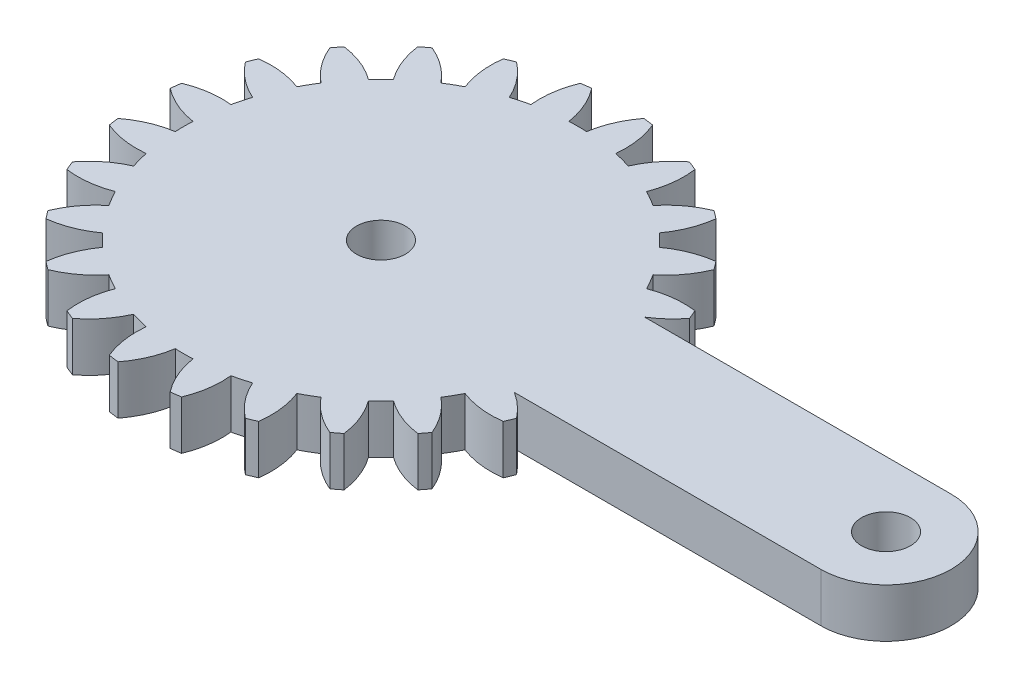
SolidWorks part; units mm, degrees
ref_plane "Front" through (0, 0, 0) normal (0, 0, 1) x (1, 0, 0)
ref_plane "Top" through (0, 0, 0) normal (0, 1, 0) x (1, 0, 0)
ref_plane "Right" through (0, 0, 0) normal (1, 0, 0) x (0, 0, -1)
sketch "Sketch1" plane through (0, 0, 0) normal (0, 1, 0) x (1, 0, 0)
  line L0 (11.068, -3.7704) -> (29.88, -3.7704)
  line L1 (29.88, 4.2296) -> (11.068, 4.2296)
  circle A0 centre (29.88, 0.2296) radius 1.5
  arc A1 (12.5081, -5.0775) -> (11.068, -3.7704) centre (8.218, -8.3571) ccw
  arc A2 (12.2692, -5.6542) -> (12.5081, -5.0775) centre (-1.12, 0.2296) ccw
  arc A3 (9.6134, -5.3407) -> (12.2692, -5.6542) centre (11.5547, -0.3017) ccw
  arc A4 (9.0707, -6.2807) -> (9.6134, -5.3407) centre (-1.12, 0.2296) ccw
  arc A5 (10.6701, -8.4239) -> (9.0707, -6.2807) centre (5.6774, -10.4814) ccw
  arc A6 (10.2901, -8.9191) -> (10.6701, -8.4239) centre (-1.12, 0.2296) ccw
  arc A7 (7.806, -7.9289) -> (10.2901, -8.9191) centre (10.9853, -3.564) ccw
  arc A8 (7.0385, -8.6964) -> (7.806, -7.9289) centre (-1.12, 0.2296) ccw
  arc A9 (8.0287, -11.1806) -> (7.0385, -8.6964) centre (2.6736, -11.8757) ccw
  arc A10 (7.5335, -11.5605) -> (8.0287, -11.1806) centre (-1.12, 0.2296) ccw
  arc A11 (5.3903, -9.9611) -> (7.5335, -11.5605) centre (9.591, -6.5678) ccw
  arc A12 (4.4502, -10.5038) -> (5.3903, -9.9611) centre (-1.12, 0.2296) ccw
  arc A13 (4.7638, -13.1596) -> (4.4502, -10.5038) centre (-0.5887, -12.4451) ccw
  arc A14 (4.1871, -13.3985) -> (4.7638, -13.1596) centre (-1.12, 0.2296) ccw
  arc A15 (2.5309, -11.2988) -> (4.1871, -13.3985) centre (7.4667, -9.1084) ccw
  arc A16 (1.4824, -11.5798) -> (2.5309, -11.2988) centre (-1.12, 0.2296) ccw
  arc A17 (1.0979, -14.2262) -> (1.4824, -11.5798) centre (-3.8873, -12.1507) ccw
  arc A18 (0.4791, -14.3077) -> (1.0979, -14.2262) centre (-1.12, 0.2296) ccw
  arc A19 (-0.5773, -11.851) -> (0.4791, -14.3077) centre (4.7572, -11.0127) ccw
  arc A20 (-1.6627, -11.851) -> (-0.5773, -11.851) centre (-1.12, 0.2296) ccw
  arc A21 (-2.7191, -14.3077) -> (-1.6627, -11.851) centre (-6.9973, -11.0127) ccw
  arc A22 (-3.338, -14.2262) -> (-2.7191, -14.3077) centre (-1.12, 0.2296) ccw
  arc A23 (-3.7225, -11.5798) -> (-3.338, -14.2262) centre (1.6473, -12.1507) ccw
  arc A24 (-4.7709, -11.2988) -> (-3.7225, -11.5798) centre (-1.12, 0.2296) ccw
  arc A25 (-6.4272, -13.3985) -> (-4.7709, -11.2988) centre (-9.7067, -9.1084) ccw
  arc A26 (-7.0038, -13.1596) -> (-6.4272, -13.3985) centre (-1.12, 0.2296) ccw
  arc A27 (-6.6903, -10.5038) -> (-7.0038, -13.1596) centre (-1.6513, -12.4451) ccw
  arc A28 (-7.6303, -9.9611) -> (-6.6903, -10.5038) centre (-1.12, 0.2296) ccw
  arc A29 (-9.7735, -11.5605) -> (-7.6303, -9.9611) centre (-11.831, -6.5678) ccw
  arc A30 (-10.2687, -11.1806) -> (-9.7735, -11.5605) centre (-1.12, 0.2296) ccw
  arc A31 (-9.2785, -8.6964) -> (-10.2687, -11.1806) centre (-4.9137, -11.8757) ccw
  arc A32 (-10.046, -7.9289) -> (-9.2785, -8.6964) centre (-1.12, 0.2296) ccw
  arc A33 (-12.5302, -8.9191) -> (-10.046, -7.9289) centre (-13.2254, -3.564) ccw
  arc A34 (-12.9102, -8.4239) -> (-12.5302, -8.9191) centre (-1.12, 0.2296) ccw
  arc A35 (-11.3107, -6.2807) -> (-12.9102, -8.4239) centre (-7.9175, -10.4814) ccw
  arc A36 (-11.8535, -5.3407) -> (-11.3107, -6.2807) centre (-1.12, 0.2296) ccw
  arc A37 (-14.5093, -5.6542) -> (-11.8535, -5.3407) centre (-13.7947, -0.3017) ccw
  arc A38 (-14.7481, -5.0775) -> (-14.5093, -5.6542) centre (-1.12, 0.2296) ccw
  arc A39 (-12.6485, -3.4213) -> (-14.7481, -5.0775) centre (-10.4581, -8.3571) ccw
  arc A40 (-12.9294, -2.3728) -> (-12.6485, -3.4213) centre (-1.12, 0.2296) ccw
  arc A41 (-15.5759, -1.9883) -> (-12.9294, -2.3728) centre (-13.5004, 2.9969) ccw
  arc A42 (-15.6573, -1.3695) -> (-15.5759, -1.9883) centre (-1.12, 0.2296) ccw
  arc A43 (-13.2006, -0.3131) -> (-15.6573, -1.3695) centre (-12.3623, -5.6476) ccw
  arc A44 (-13.2006, 0.7723) -> (-13.2006, -0.3131) centre (-1.12, 0.2296) ccw
  arc A45 (-15.6573, 1.8287) -> (-13.2006, 0.7723) centre (-12.3623, 6.1069) ccw
  arc A46 (-15.5759, 2.4475) -> (-15.6573, 1.8287) centre (-1.12, 0.2296) ccw
  arc A47 (-12.9294, 2.8321) -> (-15.5759, 2.4475) centre (-13.5004, -2.5377) ccw
  arc A48 (-12.6485, 3.8805) -> (-12.9294, 2.8321) centre (-1.12, 0.2296) ccw
  arc A49 (-14.7481, 5.5368) -> (-12.6485, 3.8805) centre (-10.4581, 8.8163) ccw
  arc A50 (-14.5093, 6.1134) -> (-14.7481, 5.5368) centre (-1.12, 0.2296) ccw
  arc A51 (-11.8535, 5.7999) -> (-14.5093, 6.1134) centre (-13.7947, 0.7609) ccw
  arc A52 (-11.3107, 6.7399) -> (-11.8535, 5.7999) centre (-1.12, 0.2296) ccw
  arc A53 (-12.9102, 8.8831) -> (-11.3107, 6.7399) centre (-7.9175, 10.9406) ccw
  arc A54 (-12.5302, 9.3783) -> (-12.9102, 8.8831) centre (-1.12, 0.2296) ccw
  arc A55 (-10.046, 8.3881) -> (-12.5302, 9.3783) centre (-13.2254, 4.0233) ccw
  arc A56 (-9.2785, 9.1556) -> (-10.046, 8.3881) centre (-1.12, 0.2296) ccw
  arc A57 (-10.2687, 11.6398) -> (-9.2785, 9.1556) centre (-4.9137, 12.3349) ccw
  arc A58 (-9.7735, 12.0198) -> (-10.2687, 11.6398) centre (-1.12, 0.2296) ccw
  arc A59 (-7.6303, 10.4203) -> (-9.7735, 12.0198) centre (-11.831, 7.0271) ccw
  arc A60 (-6.6903, 10.9631) -> (-7.6303, 10.4203) centre (-1.12, 0.2296) ccw
  arc A61 (-7.0038, 13.6188) -> (-6.6903, 10.9631) centre (-1.6513, 12.9043) ccw
  arc A62 (-6.4272, 13.8577) -> (-7.0038, 13.6188) centre (-1.12, 0.2296) ccw
  arc A63 (-4.7709, 11.7581) -> (-6.4272, 13.8577) centre (-9.7067, 9.5677) ccw
  arc A64 (-3.7225, 12.039) -> (-4.7709, 11.7581) centre (-1.12, 0.2296) ccw
  arc A65 (-3.338, 14.6855) -> (-3.7225, 12.039) centre (1.6473, 12.61) ccw
  arc A66 (-2.7191, 14.7669) -> (-3.338, 14.6855) centre (-1.12, 0.2296) ccw
  arc A67 (-1.6627, 12.3102) -> (-2.7191, 14.7669) centre (-6.9973, 11.4719) ccw
  arc A68 (-0.5773, 12.3102) -> (-1.6627, 12.3102) centre (-1.12, 0.2296) ccw
  arc A69 (0.4791, 14.7669) -> (-0.5773, 12.3102) centre (4.7572, 11.4719) ccw
  arc A70 (1.0979, 14.6855) -> (0.4791, 14.7669) centre (-1.12, 0.2296) ccw
  arc A71 (1.4824, 12.039) -> (1.0979, 14.6855) centre (-3.8873, 12.61) ccw
  arc A72 (2.5309, 11.7581) -> (1.4824, 12.039) centre (-1.12, 0.2296) ccw
  arc A73 (4.1871, 13.8577) -> (2.5309, 11.7581) centre (7.4667, 9.5677) ccw
  arc A74 (4.7638, 13.6188) -> (4.1871, 13.8577) centre (-1.12, 0.2296) ccw
  arc A75 (4.4502, 10.9631) -> (4.7638, 13.6188) centre (-0.5887, 12.9043) ccw
  arc A76 (5.3903, 10.4203) -> (4.4502, 10.9631) centre (-1.12, 0.2296) ccw
  arc A77 (7.5335, 12.0198) -> (5.3903, 10.4203) centre (9.591, 7.0271) ccw
  arc A78 (8.0287, 11.6398) -> (7.5335, 12.0198) centre (-1.12, 0.2296) ccw
  arc A79 (7.0385, 9.1556) -> (8.0287, 11.6398) centre (2.6736, 12.3349) ccw
  arc A80 (7.806, 8.3881) -> (7.0385, 9.1556) centre (-1.12, 0.2296) ccw
  arc A81 (10.2901, 9.3783) -> (7.806, 8.3881) centre (10.9853, 4.0233) ccw
  arc A82 (10.6701, 8.8831) -> (10.2901, 9.3783) centre (-1.12, 0.2296) ccw
  arc A83 (9.0707, 6.7399) -> (10.6701, 8.8831) centre (5.6774, 10.9406) ccw
  arc A84 (9.6134, 5.7999) -> (9.0707, 6.7399) centre (-1.12, 0.2296) ccw
  arc A85 (12.2692, 6.1134) -> (9.6134, 5.7999) centre (11.5547, 0.7609) ccw
  arc A86 (12.5081, 5.5368) -> (12.2692, 6.1134) centre (-1.12, 0.2296) ccw
  arc A87 (11.068, 4.2296) -> (12.5081, 5.5368) centre (8.218, 8.8163) ccw
  arc A88 (29.88, -3.7704) -> (29.88, 4.2296) centre (29.88, 0.2296) ccw
  circle A89 centre (-1.12, 0.2296) radius 1.5
extrude "Boss-Extrude1" add sketch "Sketch1" along normal mid plane 3
